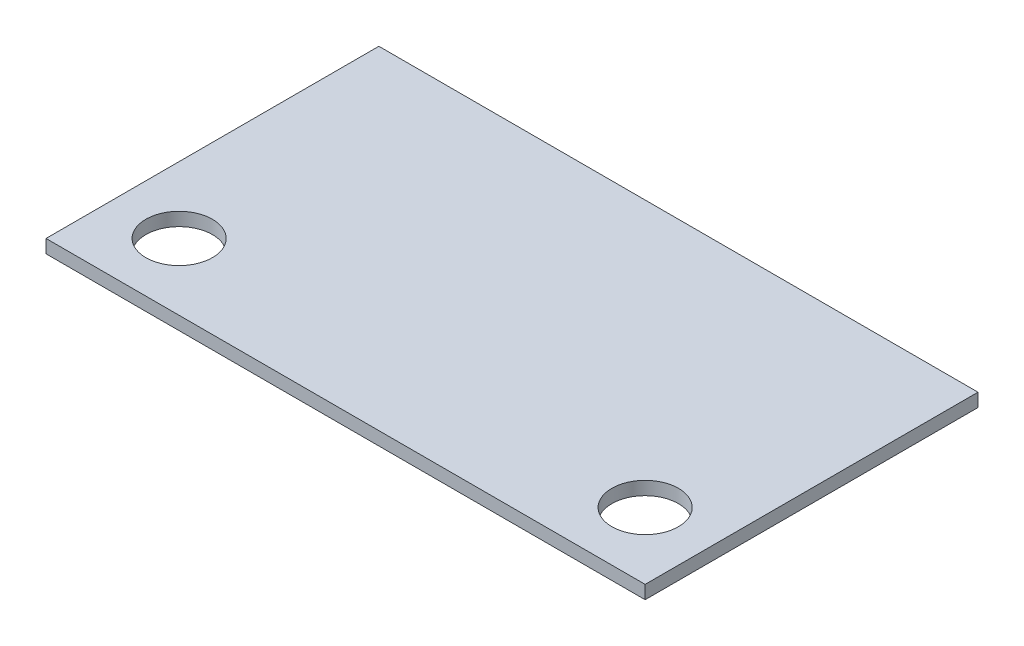
SolidWorks part; units mm, degrees
ref_plane "Front Plane" through (0, 0, 0) normal (0, 0, 1) x (1, 0, 0)
ref_plane "Top Plane" through (0, 0, 0) normal (0, 1, 0) x (1, 0, 0)
ref_plane "Right Plane" through (0, 0, 0) normal (1, 0, 0) x (0, 0, -1)
sketch "Sketch1" plane through (0, 0, 0) normal (0, 1, 0) x (1, 0, 0)
  line L1 (-37.5397, 18.9683) -> (52.4603, 18.9683)
  line L2 (-37.5397, 18.9683) -> (-37.5397, -31.0317)
  line L3 (-37.5397, -31.0317) -> (52.4603, -31.0317)
  line L4 (52.4603, 18.9683) -> (52.4603, -31.0317)
  circle A0 centre (-27.5397, -21.0317) radius 5
  circle A1 centre (42.4603, -21.0317) radius 5
  dimension "D3" = 10
  dimension "D4" = 10
  dimension "D5" = 10
  dimension "D1" = 90
  dimension "D2" = 50
  dimension "D6" = 10
extrude "Boss-Extrude1" add sketch "Sketch1" along normal blind 2
